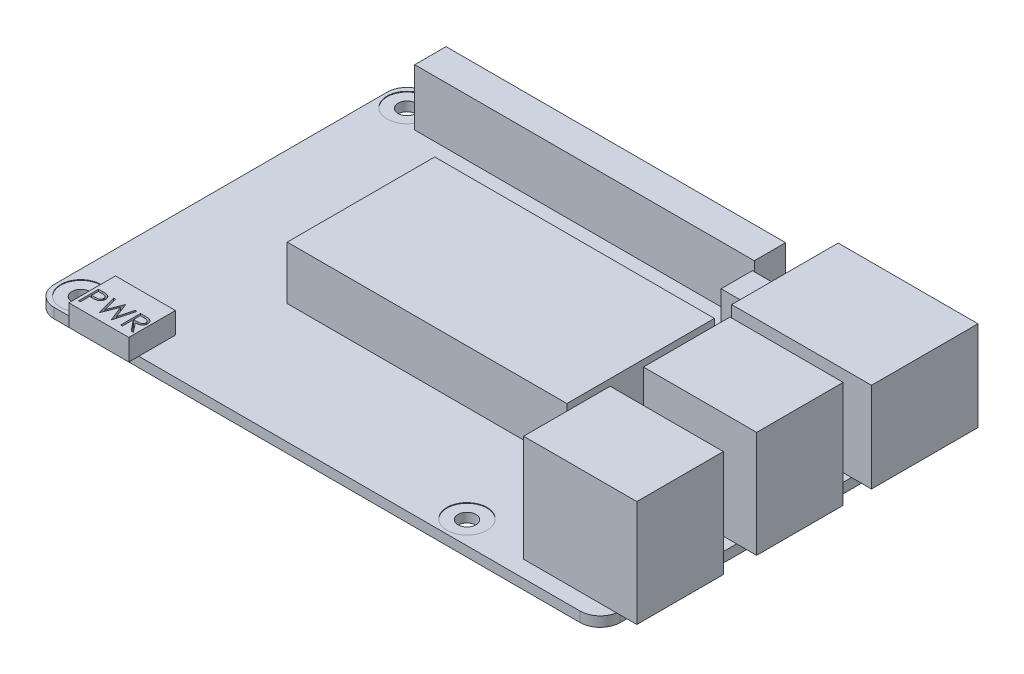
SolidWorks part; units mm, degrees
ref_plane "Front Plane" through (0, 0, 0) normal (0, 0, 1) x (1, 0, 0)
ref_plane "Top Plane" through (0, 0, 0) normal (0, 1, 0) x (1, 0, 0)
ref_plane "Right Plane" through (0, 0, 0) normal (1, 0, 0) x (0, 0, -1)
sketch "Sketch1" plane through (0, 0, 0) normal (0, 1, 0) x (1, 0, 0)
  line L0 (3.5, 52.5) -> (61.5, 52.5) construction
  line L1 (0, 0) -> (85, 0)
  line L2 (0, 0) -> (0, 56)
  line L3 (0, 56) -> (85, 56)
  line L4 (85, 0) -> (85, 56)
  line L5 (61.5, 52.5) -> (61.5, 3.5) construction
  line L6 (61.5, 3.5) -> (3.5, 3.5) construction
  line L7 (3.5, 3.5) -> (3.5, 52.5) construction
  circle A0 centre (3.5, 52.5) radius 1.35
  circle A1 centre (3.5, 3.5) radius 1.35
  circle A2 centre (61.5, 3.5) radius 1.35
  circle A3 centre (61.5, 52.5) radius 1.35
  dimension "D5" = 2.7
  dimension "D6" = 3.5
  dimension "D7" = 3.5
  dimension "D1" = 85
  dimension "D2" = 56
  dimension "D3" = 58
  dimension "D4" = 49
extrude "Boss-Extrude1" add sketch "Sketch1" along normal blind 1.5
fillet "Fillet1" radius 3 4 edges at (85, 0.75, -56) (85, 0.75, 0) (0, 0.75, -56) (0, 0.75, 0)
sketch "Sketch2" plane through (0, 1.5, 0) normal (0, 1, 0) x (1, 0, 0)
  line L0 (3, 0) -> (82, 0) construction
  line L1 (88, 20.5) -> (71, 20.5)
  line L2 (88, 20.5) -> (88, 33.5)
  line L3 (88, 33.5) -> (71, 33.5)
  line L4 (71, 20.5) -> (71, 33.5)
  line L5 (88, 2.5) -> (71, 2.5)
  line L6 (88, 2.5) -> (88, 15.5)
  line L7 (88, 15.5) -> (71, 15.5)
  line L8 (71, 2.5) -> (71, 15.5)
  line L9 (85, 3) -> (85, 53) construction
  point P8 (88, 9)
  point P11 (88, 27)
  dimension "D1" = 17
  dimension "D2" = 13
  dimension "D3" = 9
  dimension "D4" = 27
  dimension "D5" = 3
extrude "Boss-Extrude2" add sketch "Sketch2" along normal blind 16
sketch "Sketch3" plane through (0, 1.5, 0) normal (0, 1, 0) x (1, 0, 0)
  line L0 (88, 20.5) -> (88, 33.5) construction
  line L1 (88, 37.75) -> (67, 37.75)
  line L2 (88, 37.75) -> (88, 53.75)
  line L3 (88, 53.75) -> (67, 53.75)
  line L4 (67, 37.75) -> (67, 53.75)
  line L5 (3, 0) -> (82, 0) construction
  point P6 (88, 45.75)
  dimension "D1" = 21
  dimension "D2" = 16
  dimension "D3" = 45.75
extrude "Boss-Extrude3" add sketch "Sketch3" along normal blind 13.5
sketch "Sketch4" plane through (0, 1.5, 0) normal (0, 1, 0) x (1, 0, 0)
  line L0 (61.5, 52.5) -> (61.5, 48.71) construction
  line L1 (7, 54.85) -> (58, 54.85)
  line L2 (7, 54.85) -> (7, 50.15)
  line L3 (7, 50.15) -> (58, 50.15)
  line L4 (58, 54.85) -> (58, 50.15)
  line L5 (59.15, 48.71) -> (63.85, 48.71)
  line L6 (59.15, 48.71) -> (59.15, 44.01)
  line L7 (59.15, 44.01) -> (63.85, 44.01)
  line L8 (63.85, 48.71) -> (63.85, 44.01)
  line L9 (3.5, 52.5) -> (61.5, 52.5) construction
  point P11 (63.85, 46.36)
  point P13 (32.5, 52.5)
  point P15 (32.5, 54.85)
  point P16 (7, 52.5)
  dimension "D1" = 6.14
  dimension "D2" = 51
  dimension "D3" = 4.7
  dimension "D4" = 4.7
extrude "Boss-Extrude4" add sketch "Sketch4" along normal blind 8.5
sketch "Sketch5" plane through (0, 1.5, 0) normal (0, 1, 0) x (1, 0, 0)
  line L0 (3, 0) -> (82, 0) construction
  line L1 (6.7, -1.5) -> (15.7, -1.5)
  line L2 (6.7, -1.5) -> (6.7, 5.5)
  line L3 (6.7, 5.5) -> (15.7, 5.5)
  line L4 (15.7, -1.5) -> (15.7, 5.5)
  circle A0 centre (3.5, 3.5) radius 1.35 construction
  point P8 (11.2, -1.5)
  dimension "D4" = 7.7
  dimension "D1" = 9
  dimension "D2" = 7
  dimension "D3" = 1.5
extrude "Boss-Extrude5" add sketch "Sketch5" along normal blind 3.2
sketch "Sketch6" plane through (0, 4.7, 0) normal (0, 1, 0) x (1, 0, 0)
  line L0 (6.7, -0.5) -> (15.7, -0.5) construction
  line L1 (6.7, 5.5) -> (6.7, -1.5) construction
  line L2 (15.7, -1.5) -> (15.7, 5.5) construction
  line L3 (6.7, -1.5) -> (15.7, -1.5) construction
  text T0 "PWR" font "Century Gothic" height 3
  dimension "D1" = 1
extrude "Cut-Extrude1" cut sketch "Sketch6" against normal blind 1
sketch "Sketch7" plane through (0, 1.5, 0) normal (0, 1, 0) x (1, 0, 0)
  line L0 (0, 53) -> (0, 3) construction
  line L5 (62, 18) -> (20, 18)
  line L6 (62, 18) -> (62, 40.15)
  line L7 (62, 40.15) -> (20, 40.15)
  line L8 (20, 18) -> (20, 40.15)
  line L9 (67, 53.75) -> (67, 37.75) construction
  line L10 (7, 50.15) -> (58, 50.15) construction
  line L11 (15.7, 0) -> (82, 0) construction
  dimension "D1" = 20
  dimension "D2" = 5
  dimension "D3" = 10
  dimension "D4" = 18
extrude "Boss-Extrude6" add sketch "Sketch7" along normal blind 8
sketch "Sketch8" plane through (0, 10, 0) normal (0, 1, 0) x (1, 0, 0)
  line L0 (7, 52.5) -> (58, 52.5)
  line L1 (7, 54.85) -> (7, 50.15) construction
  line L2 (58, 50.15) -> (58, 54.85) construction
  line L3 (9.55, 54.85) -> (9.55, 50.15)
  line L4 (7, 54.85) -> (58, 54.85)
  line L5 (7, 54.85) -> (7, 50.15)
  line L6 (7, 50.15) -> (58, 50.15)
  line L7 (58, 54.85) -> (58, 50.15)
  line L8 (12.1, 54.85) -> (12.1, 50.15)
  line L9 (14.65, 54.85) -> (14.65, 50.15)
  line L10 (17.2, 54.85) -> (17.2, 50.15)
  line L11 (19.75, 54.85) -> (19.75, 50.15)
  line L12 (22.3, 54.85) -> (22.3, 50.15)
  line L13 (24.85, 54.85) -> (24.85, 50.15)
  line L14 (27.4, 54.85) -> (27.4, 50.15)
  line L15 (29.95, 54.85) -> (29.95, 50.15)
  line L16 (32.5, 54.85) -> (32.5, 50.15)
  line L17 (35.05, 54.85) -> (35.05, 50.15)
  line L18 (37.6, 54.85) -> (37.6, 50.15)
  line L19 (40.15, 54.85) -> (40.15, 50.15)
  line L20 (42.7, 54.85) -> (42.7, 50.15)
  line L21 (45.25, 54.85) -> (45.25, 50.15)
  line L22 (47.8, 54.85) -> (47.8, 50.15)
  line L23 (50.35, 54.85) -> (50.35, 50.15)
  line L24 (52.9, 54.85) -> (52.9, 50.15)
  line L25 (55.45, 54.85) -> (55.45, 50.15)
  line L26 (9.55, 54.85) -> (12.1, 54.85) construction
  text T0 " 5V   5V                 TX   RX" font "Century Gothic" height 1
  text T1 "3V3                                                  3V3" font "Century Gothic" height 1
  dimension "D1" = 51
  dimension "D2" = 2.55
  dimension "D4" = 2.55
  dimension "D3" = 19
sketch "Sketch9" plane through (0, 1.5, 0) normal (0, 1, 0) x (1, 0, 0)
  circle A0 centre (3.5, 52.5) radius 3
  circle A1 centre (3.5, 3.5) radius 3
  circle A2 centre (61.5, 52.5) radius 3
  circle A3 centre (61.5, 3.5) radius 3
  dimension "D1" = 6
extrude "Cut-Extrude2" cut sketch "Sketch9" against normal blind 0.1
equation "\"D2@Sketch8\"=\"D1@Sketch8\"/20"
equation "\"D4@Sketch8\"=\"D2@Sketch8\""
